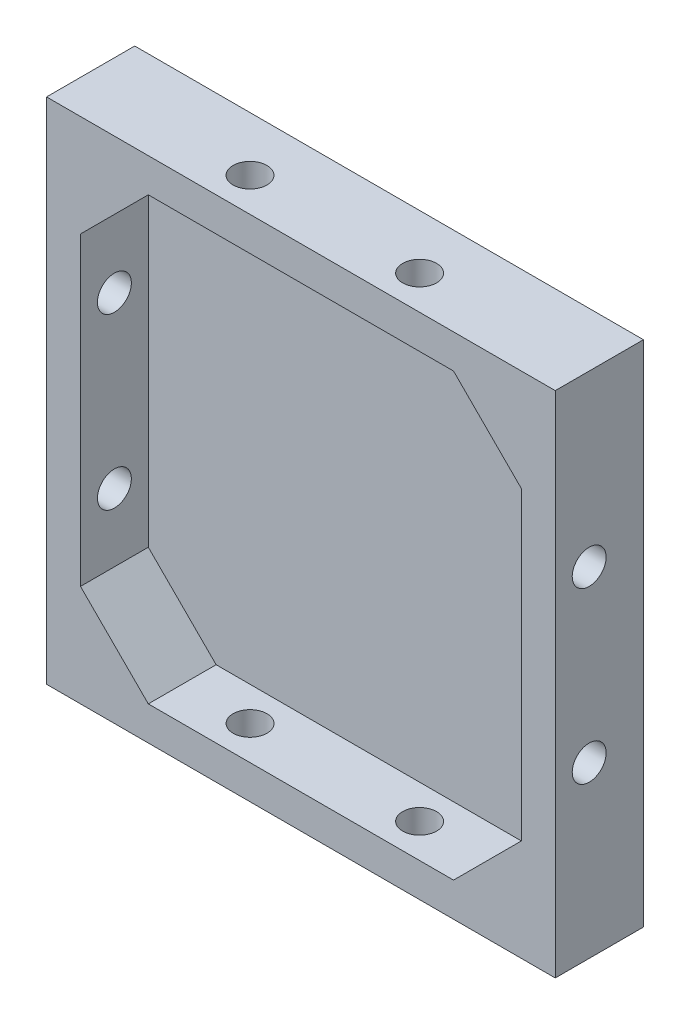
SolidWorks part; units mm, degrees
ref_plane "Plan de face" through (0, 0, 0) normal (0, 0, 1) x (1, 0, 0)
ref_plane "Plan de dessus" through (0, 0, 0) normal (0, 1, 0) x (1, 0, 0)
ref_plane "Plan de droite" through (0, 0, 0) normal (1, 0, 0) x (0, 0, -1)
sketch "Esquisse1" plane through (0, 0, 0) normal (0, 0, 1) x (1, 0, 0)
  line L0 (44.1184, 33.7284) -> (54.1184, 33.7284)
  line L1 (-20.8816, 33.7284) -> (44.1184, 33.7284)
  line L2 (-20.8816, 33.7284) -> (-20.8816, -41.2716)
  line L3 (-20.8816, -41.2716) -> (54.1184, -41.2716)
  line L4 (54.1184, 23.7284) -> (54.1184, -41.2716)
  line L5 (54.1184, 33.7284) -> (54.1184, 23.7284)
  point P6 (54.1184, 33.7284)
  dimension "D1" = 75
  dimension "D2" = 75
extrude "Boss.-Extru.1" add sketch "Esquisse1" along normal blind 13
shell "Coque1" thickness 5
sketch "Esquisse2" plane through (-20.8816, 0, 0) normal (-1, 0, 0) x (0, 0, 1)
  line L0 (13, 33.7284) -> (13, -41.2716) construction
  line L1 (13, 33.7284) -> (0, 33.7284) construction
  line L2 (13, -41.2716) -> (0, -41.2716) construction
  circle A0 centre (8, 8.7284) radius 2.5
  circle A1 centre (8, -16.2716) radius 2.5
  dimension "D1" = 5
  dimension "D2" = 5
  dimension "D3" = 5
  dimension "D4" = 5
  dimension "D5" = 25
  dimension "D6" = 25
extrude "Enlèv. mat.-Extru.1" cut sketch "Esquisse2" against normal up to surface (75 mm away) contours A1 | A0 up to face at (54.1184, -3.7716, 6.5)
sketch "Esquisse3" plane through (0, -41.2716, 0) normal (0, -1, 0) x (1, 0, 0)
  line L0 (-20.8816, 13) -> (54.1184, 13) construction
  line L2 (54.1184, 13) -> (54.1184, 0) construction
  line L3 (-20.8816, 13) -> (-20.8816, 0) construction
  circle A0 centre (4.1184, 8) radius 2.5
  circle A1 centre (29.1184, 8) radius 2.5
  dimension "D1" = 5
  dimension "D2" = 5
  dimension "D3" = 5
  dimension "D4" = 5
  dimension "D5" = 25
  dimension "D6" = 25
extrude "Enlèv. mat.-Extru.2" cut sketch "Esquisse3" against normal up to surface (75 mm away) up to face at (16.6184, 33.7284, 6.5)
sketch "Esquisse4" plane through (0, 0, 3) normal (0, 0, 1) x (1, 0, 0)
  line L0 (-5.8816, 28.7284) -> (-15.8816, 18.7284)
  line L1 (49.1184, 28.7284) -> (-15.8816, 28.7284) construction
  line L2 (-15.8816, 28.7284) -> (-15.8816, -36.2716) construction
  line L3 (-15.8816, 18.7284) -> (-15.8816, 28.7284)
  line L4 (-15.8816, 28.7284) -> (-5.8816, 28.7284)
  line L5 (49.1184, 28.7284) -> (49.1184, 18.7284)
  line L6 (49.1184, -36.2716) -> (49.1184, 28.7284) construction
  line L7 (49.1184, 18.7284) -> (39.1184, 28.7284)
  line L8 (39.1184, 28.7284) -> (49.1184, 28.7284)
  line L9 (49.1184, 28.7284) -> (-15.8816, 28.7284) construction
  line L10 (49.1184, -36.2716) -> (49.1184, -26.2716)
  line L11 (49.1184, -26.2716) -> (39.1184, -36.2716)
  line L12 (-15.8816, -36.2716) -> (49.1184, -36.2716) construction
  line L13 (39.1184, -36.2716) -> (49.1184, -36.2716)
  line L14 (-5.8816, -36.2716) -> (-15.8816, -26.2716)
  line L15 (-15.8816, 28.7284) -> (-15.8816, -36.2716) construction
  line L16 (-15.8816, -26.2716) -> (-15.8816, -36.2716)
  line L17 (-15.8816, -36.2716) -> (-5.8816, -36.2716)
  dimension "D1" = 10
  dimension "D2" = 10
  dimension "D3" = 10
  dimension "D4" = 10
  dimension "D5" = 10
  dimension "D6" = 10
  dimension "D7" = 10
  dimension "D8" = 10
extrude "Boss.-Extru.2" add sketch "Esquisse4" along normal up to surface (10 mm away) up to face at (16.6184, -3.7716, 13)
